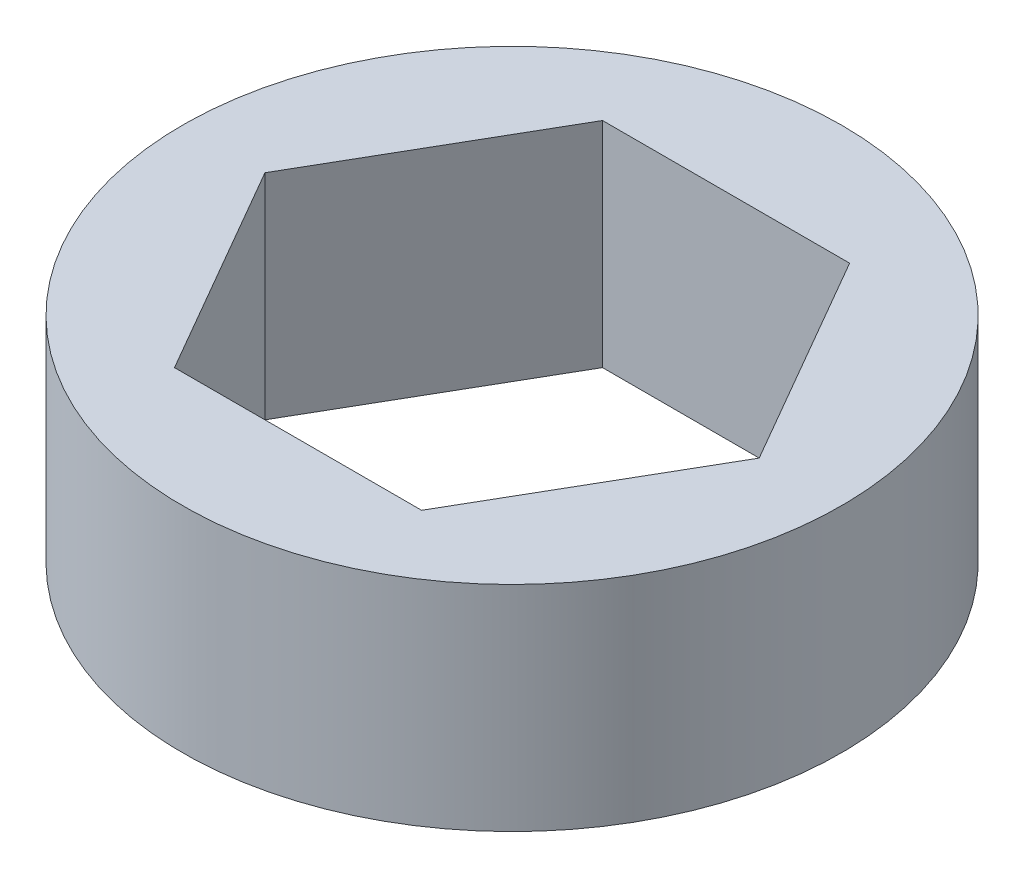
SolidWorks part; units mm, degrees
material "Nylon 101"
ref_plane "Front Plane" through (0, 0, 0) normal (0, 0, 1) x (1, 0, 0)
ref_plane "Top Plane" through (0, 0, 0) normal (0, 1, 0) x (1, 0, 0)
ref_plane "Right Plane" through (0, 0, 0) normal (1, 0, 0) x (0, 0, -1)
sketch "Sketch1" plane through (0, 0, 0) normal (0, 1, 0) x (1, 0, 0)
  line L1 (-3.6662, 6.35) -> (-7.3323, 0)
  line L2 (-7.3323, 0) -> (-3.6662, -6.35)
  line L3 (-3.6662, -6.35) -> (3.6662, -6.35)
  line L4 (3.6662, -6.35) -> (7.3323, 0)
  line L5 (7.3323, 0) -> (3.6662, 6.35)
  line L6 (3.6662, 6.35) -> (-3.6662, 6.35)
  circle A0 centre (0, 0) radius 9.779
  circle A1 centre (0, 0) radius 6.35 construction
  dimension "D1" = 12.7
  dimension "D2" = 19.558
extrude "Boss-Extrude1" add sketch "Sketch1" against normal mid plane 6.35
equation "\"Length\"= 0.25"
equation "\"D1@Boss-Extrude1\"=\"Length\""
